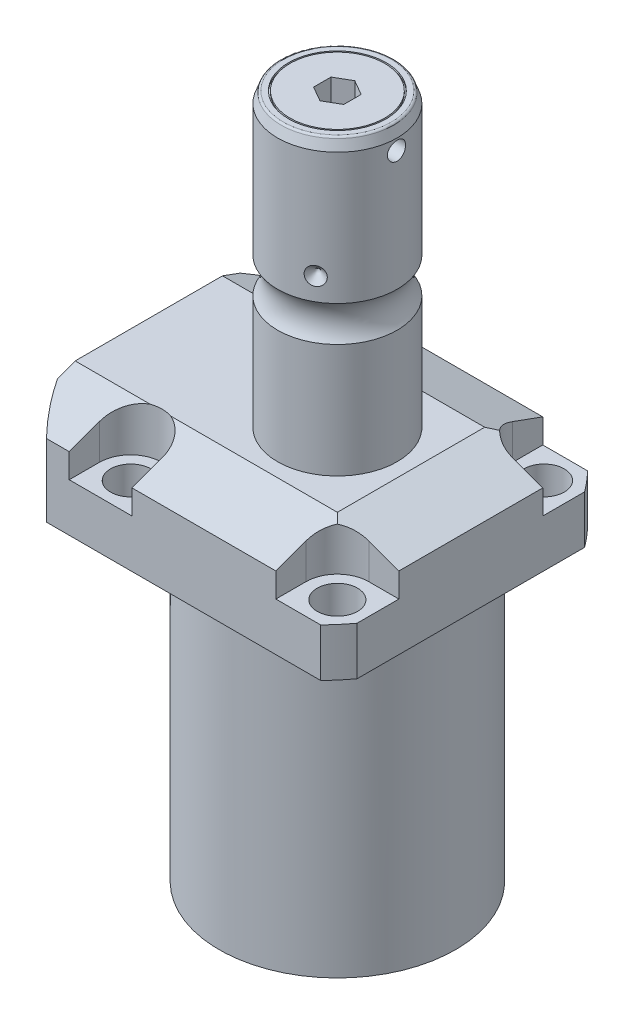
SolidWorks part; units mm, degrees
material "Alloy Steel"
ref_plane "Front Plane" through (0, 0, 0) normal (0, 0, 1) x (1, 0, 0)
ref_plane "Top Plane" through (0, 0, 0) normal (0, 1, 0) x (1, 0, 0)
ref_plane "Right Plane" through (0, 0, 0) normal (1, 0, 0) x (0, 0, -1)
sketch "Sketch1" plane through (0, 0, 0) normal (0, -1, 0) x (0, 0, 1)
  line L0 (-35.433, 50.063) -> (35.433, 50.063)
  line L1 (35.433, 50.063) -> (35.433, -35.433)
  line L2 (35.433, -35.433) -> (-35.433, -35.433)
  line L3 (-35.433, -35.433) -> (-35.433, 50.063)
  line L4 (0, 0) -> (0, -60.6467) construction
  dimension "D1" = 35.433
  dimension "D2" = 85.496
  dimension "D3" = 70.866
extrude "Extrude1" add sketch "Sketch1" against normal blind 104.4448
sketch "Sketch2" plane through (0, 0, 0) normal (0, -1, 0) x (1, 0, 0)
  circle A0 centre (-5.4102, 0) radius 50.8
  dimension "D1" = 101.6
  dimension "D2" = 5.4102
extrude "Cut-Extrude1" cut sketch "Sketch2" against normal through all flip side to cut
sketch "Sketch3" plane through (0, 0, 0) normal (1, 0, 0) x (0, 0, -1)
  line L0 (31.3945, 0) -> (31.3945, 79.4258)
  line L1 (31.3945, 79.4258) -> (76.5937, 79.4258)
  line L2 (76.5937, 79.4258) -> (76.5937, 0)
  line L3 (76.5937, 0) -> (31.3945, 0)
  line L4 (0, -93.345) -> (0, 4.445) construction
  line L5 (24.2233, 0) -> (-24.2233, 0) construction
  dimension "D1" = 62.789
  dimension "D2" = 153.1874
  dimension "D3" = 79.4258
revolve "Cut-Revolve1" cut sketch "Sketch3" angle 360 about L4
fillet "Fillet1" radius 0.381 1 edges at (0, 79.4258, -31.3945)
sketch "Sketch4" plane through (0, 104.4448, 0) normal (0, 1, 0) x (-1, 0, 0)
  line L0 (-35.433, -30.2072) -> (-35.433, 30.2072) construction
  line L1 (41.8127, 35.433) -> (-30.9923, 35.433) construction
  line L2 (-19.1008, -35.433) -> (-19.1008, -27.432)
  line L3 (-35.433, -35.433) -> (-19.1008, -35.433)
  line L4 (-35.433, -19.1008) -> (-35.433, -35.433)
  line L5 (-27.432, -19.1008) -> (-35.433, -19.1008)
  line L6 (35.7632, -35.433) -> (19.1008, -35.433)
  line L7 (19.1008, 35.433) -> (19.1008, 27.432)
  line L8 (35.7632, 35.433) -> (35.7632, 27.432)
  line L9 (35.7632, 35.433) -> (19.1008, 35.433)
  line L10 (-27.432, 19.1008) -> (-35.433, 19.1008)
  line L11 (-35.433, 19.1008) -> (-35.433, 35.433)
  line L12 (-35.433, 35.433) -> (-19.1008, 35.433)
  line L13 (-19.1008, 35.433) -> (-19.1008, 27.432)
  line L14 (-48.9217, 0) -> (49.4551, 0) construction
  line L15 (35.7632, -35.433) -> (35.7632, -27.432)
  line L16 (19.1008, -35.433) -> (19.1008, -27.432)
  arc A0 (19.1008, -27.432) -> (35.7632, -27.432) centre (27.432, -27.432) cw
  arc A1 (-27.432, -19.1008) -> (-19.1008, -27.432) centre (-27.432, -27.432) cw
  arc A2 (-27.432, 19.1008) -> (-19.1008, 27.432) centre (-27.432, 27.432) ccw
  arc A3 (19.1008, 27.432) -> (35.7632, 27.432) centre (27.432, 27.432) ccw
  dimension "D2" = 8.3312
  dimension "D1" = 27.432
  dimension "D3" = 27.432
  dimension "D4" = 54.864
extrude "Cut-Extrude2" cut sketch "Sketch4" against normal blind 12.243
sketch "Sketch5" plane through (0, 0, 0) normal (1, 0, 0) x (0, 0, -1)
  line L0 (-19.558, 104.4448) -> (-35.433, 98.6668)
  line L1 (0, 0) -> (0, 154.1081) construction
  line L2 (-19.558, 104.4448) -> (-35.433, 104.4448)
  line L3 (-35.433, 104.4448) -> (-35.433, 98.6668)
  dimension "D1" = 15.875
  dimension "D2" = 20
extrude "Cut-Extrude9" cut sketch "Sketch5" against normal through all and the other way through all
mirror "Mirror1" about plane through (0, 0, 0) normal (0, 0, 1) of "Cut-Extrude9"
sketch "Sketch9" plane through (0, 0, 0) normal (0, 0, 1) x (1, 0, 0)
  line L0 (19.558, 104.4448) -> (35.433, 98.6668)
  line L1 (35.433, 98.6668) -> (35.433, 104.4448)
  line L2 (35.433, 104.4448) -> (19.558, 104.4448)
  dimension "D1" = 15.875
  dimension "D2" = 20
extrude "Cut-Extrude7" cut sketch "Sketch9" against normal through all and the other way through all
ref_plane "Plane14" through (-35.0774, 0, 0) normal (1, 0, 0) x (0, 0, -1)
sketch "Sketch20" plane through (-35.0774, 88.9, -18.1102) normal (1, 0, 0) x (0, 1, 0)
  line L0 (-88.9, 18.1102) -> (39.8401, 18.1102) construction
  line L1 (-7.2797, 32.639) -> (36.9042, 32.639) construction
  line L2 (-9.4742, 38.3413) -> (-8.0264, 38.3413)
  line L3 (-9.4742, -6.1131) -> (-9.4742, 42.3335) construction
  line L4 (-8.0264, 38.3413) -> (-8.0264, 35.8902)
  line L5 (-8.0264, 35.8902) -> (-7.0104, 35.8902)
  line L6 (-7.0104, 35.8902) -> (-7.0104, 33.8836)
  line L7 (-7.0104, 33.8836) -> (3.9624, 33.8836)
  line L8 (3.9624, 33.8836) -> (3.9624, 32.639)
  line L9 (3.9624, 32.639) -> (-9.4742, 32.639)
  line L10 (-9.4742, 38.3413) -> (-9.4742, 32.639)
  dimension "D1" = 14.5288
  dimension "D2" = 11.4046
  dimension "D3" = 1.4478
  dimension "D4" = 6.5024
  dimension "D5" = 1.016
  dimension "D6" = 2.4892
  dimension "D7" = 10.9728
revolve "Cut-Revolve4" cut sketch "Sketch20" angle 360 about L1
mirror "Mirror10" about plane through (0, 0, 0) normal (0, 0, 1) of "Cut-Revolve4"
sketch "Sketch10" plane through (-35.0774, 88.9, -18.1102) normal (1, 0, 0) x (0, 1, 0)
  line L0 (-1.0325, 3.5814) -> (1.5659, 3.5814) construction
  line L1 (3.9624, 4.826) -> (-7.0104, 4.826) construction
  line L2 (-7.0104, 2.3368) -> (3.9624, 2.3368) construction
  line L4 (-9.4742, -12.097) -> (-9.4742, 48.3174) construction
  circle A0 centre (-9.2075, 8.1026) radius 1.1811
  dimension "D1" = 2.3622
  dimension "D2" = 0.2667
  dimension "D3" = 9.0424
revolve "Revolve4" add sketch "Sketch10" angle 360 about L0
mirror "Mirror12" about plane through (0, 0, 0) normal (0, 0, 1) of bodies 135
sketch "Sketch15" plane through (0, 0, 0) normal (1, 0, 0) x (0, 0, -1)
  line L0 (0, 104.4448) -> (15.875, 104.4448)
  line L1 (15.875, 104.4448) -> (15.875, 134.6881)
  line L2 (15.875, 144.1023) -> (15.875, 178.8922)
  line L3 (14.8118, 181.8132) -> (0, 181.8132)
  line L4 (0, 181.8132) -> (0, 104.4448)
  line L5 (0, 250.2908) -> (0, 28.9095) construction
  line L6 (19.558, 104.4448) -> (-19.558, 104.4448) construction
  line L7 (14.8118, 181.8132) -> (15.875, 178.8922)
  arc A0 (15.875, 144.1023) -> (15.875, 134.6881) centre (22.2504, 139.3952) ccw
  dimension "D2" = 20
  dimension "D4" = 7.9248
  dimension "D6" = 28.6512
  dimension "D1" = 102.3874
  dimension "D3" = 31.75
  dimension "D5" = 42.418
  dimension "D7" = 2.921
revolve "Revolve3" add sketch "Sketch15" angle 360 about L5
hole_wizard "Hole1" positions "Sketch18" profile "Sketch17" legacy end condition up to next
sketch "Sketch18" plane through (0, 92.2018, 0) normal (0, 1, 0) x (-1, 0, 0)
  arc A0 (35.7632, -27.432) -> (19.1008, -27.432) centre (27.432, -27.432) ccw construction
  arc A1 (19.1008, 27.432) -> (35.7632, 27.432) centre (27.432, 27.432) ccw construction
  arc A2 (-27.432, 19.1008) -> (-19.1008, 27.432) centre (-27.432, 27.432) ccw construction
  arc A3 (-19.1008, -27.432) -> (-27.432, -19.1008) centre (-27.432, -27.432) ccw construction
  point P0 (-27.432, -27.432)
  point P1 (-27.432, 27.432)
  point P3 (27.432, 27.432)
  point P5 (27.432, -27.432)
sketch "Sketch17" plane through (27.432, 92.2018, -27.432) normal (1, 0, 0) x (0, 0, 1)
  line L0 (0, 0) -> (0, 12.776)
  line L1 (0, 12.776) -> (5.3594, 12.776)
  line L2 (5.3594, 12.776) -> (5.3594, 0)
  line L3 (5.3594, 0) -> (0, 0)
  line L4 (0, 110) -> (0, -10) construction
  dimension "Diameter" = 10.7188
  dimension "Depth" = 12.776
chamfer "Chamfer1" distance 0.635 angle 45 2 edges at (-35.0774, 81.8896, 13.2842) (-35.0774, 81.8896, -13.2842)
ref_plane "Plane15" through (0, 91.9226, 0) normal (0, -1, 0) x (1, 0, 0)
sketch "Sketch21" plane through (0, 91.9226, 0) normal (0, -1, 0) x (1, 0, 0)
  line L0 (-57.5495, -12.9794) -> (-2.9353, -12.9794) construction
  line L1 (-50.063, -2.5019) -> (-49.809, -2.5019)
  line L2 (-49.809, -2.5019) -> (-49.809, -6.7564)
  line L3 (-49.809, -6.7564) -> (-47.2563, -7.4404)
  line L4 (-46.6957, -8.001) -> (-30.759, -8.001)
  line L5 (-30.759, -8.001) -> (-30.759, -12.9794)
  line L6 (-30.759, -12.9794) -> (-50.063, -12.9794)
  line L7 (-50.063, 24.2233) -> (-50.063, -24.2233) construction
  line L8 (-50.063, -12.9794) -> (-50.063, -2.5019)
  line L9 (-47.2563, -7.4404) -> (-46.6957, -8.001)
  dimension "D1" = 12.9794
  dimension "D2" = 0.254
  dimension "D3" = 20.955
  dimension "D4" = 15
  dimension "D5" = 12.446
  dimension "D6" = 9.9568
  dimension "D7" = 45
  dimension "D8" = 2.5527
revolve "Cut-Revolve5" cut sketch "Sketch21" angle 360 about L0
mirror "Mirror13" about plane through (0, 0, 0) normal (0, 0, 1) of "Cut-Revolve5"
sketch "Sketch22" plane through (-49.809, 0, 0) normal (-1, 0, 0) x (0, 0, 1)
  circle A0 centre (-12.9794, 91.9226) radius 6.35
  dimension "D1" = 12.7
extrude "Extrude2" add sketch "Sketch22" along normal blind 1.651
fillet "Fillet2" radius 0.635 1 edges at (0, 181.8132, 14.8118)
sketch "Sketch24" plane through (0, 181.8132, 0) normal (0, 1, 0) x (1, 0, 0)
  circle A0 centre (0, 0) radius 12.954
  circle A1 centre (0, 0) radius 12.573
  dimension "D1" = 25.908
  dimension "D2" = 25.146
extrude "Cut-Extrude10" cut sketch "Sketch24" against normal blind 0.5
sketch "Sketch25" plane through (0, 181.8132, 0) normal (0, 1, 0) x (1, 0, 0)
  line L1 (4, -2.3094) -> (4, 2.3094)
  line L2 (4, 2.3094) -> (0, 4.6188)
  line L3 (0, 4.6188) -> (-4, 2.3094)
  line L4 (-4, 2.3094) -> (-4, -2.3094)
  line L5 (-4, -2.3094) -> (0, -4.6188)
  line L6 (0, -4.6188) -> (4, -2.3094)
  circle A0 centre (0, 0) radius 4 construction
  dimension "D1" = 8
extrude "Cut-Extrude11" cut sketch "Sketch25" against normal blind 8
sketch "Sketch26" plane through (0, 0, 0) normal (0, 0, 1) x (1, 0, 0)
  line L0 (-39.772, 150.0632) -> (35.3173, 150.0632) construction
  line L1 (-15.875, 152.4762) -> (-13.462, 150.0632)
  line L2 (-15.875, 178.8922) -> (-15.875, 144.1023) construction
  line L3 (-13.462, 150.0632) -> (-15.875, 150.0632)
  line L4 (-15.875, 150.0632) -> (-15.875, 152.4762)
  arc A0 (-15.875, 134.6881) -> (-15.875, 144.1023) centre (-22.2504, 139.3952) ccw construction
  dimension "D1" = 45
  dimension "D2" = 4.826
  dimension "D3" = 10.668
revolve "Cut-Revolve7" cut sketch "Sketch26" angle 360 about L0
pattern_circular "CirPattern1" count 3 over 360 about axis through (0, 250.2908, 0) along (0, 1, 0) of "Cut-Revolve7"
sketch "Sketch27" plane through (0, 0, 0) normal (0, 0, 1) x (1, 0, 0)
  line L0 (5.3741, 175.9712) -> (21.6654, 175.9712) construction
  line L1 (15.875, 144.1023) -> (15.875, 178.8922) construction
  line L2 (15.875, 178.3842) -> (12.065, 178.3842)
  line L3 (15.875, 178.3842) -> (15.875, 175.9712)
  line L4 (15.875, 175.9712) -> (12.065, 175.9712)
  line L5 (12.065, 178.3842) -> (12.065, 175.9712)
  line L6 (12.573, 181.8132) -> (-12.573, 181.8132) construction
  dimension "D1" = 4.826
  dimension "D2" = 3.81
  dimension "D3" = 5.842
revolve "Cut-Revolve8" cut sketch "Sketch27" angle 360 about L0
chamfer "Chamfer2" distance 1.016 angle 45 1 edges at (-51.46, 91.9226, -6.6294)
